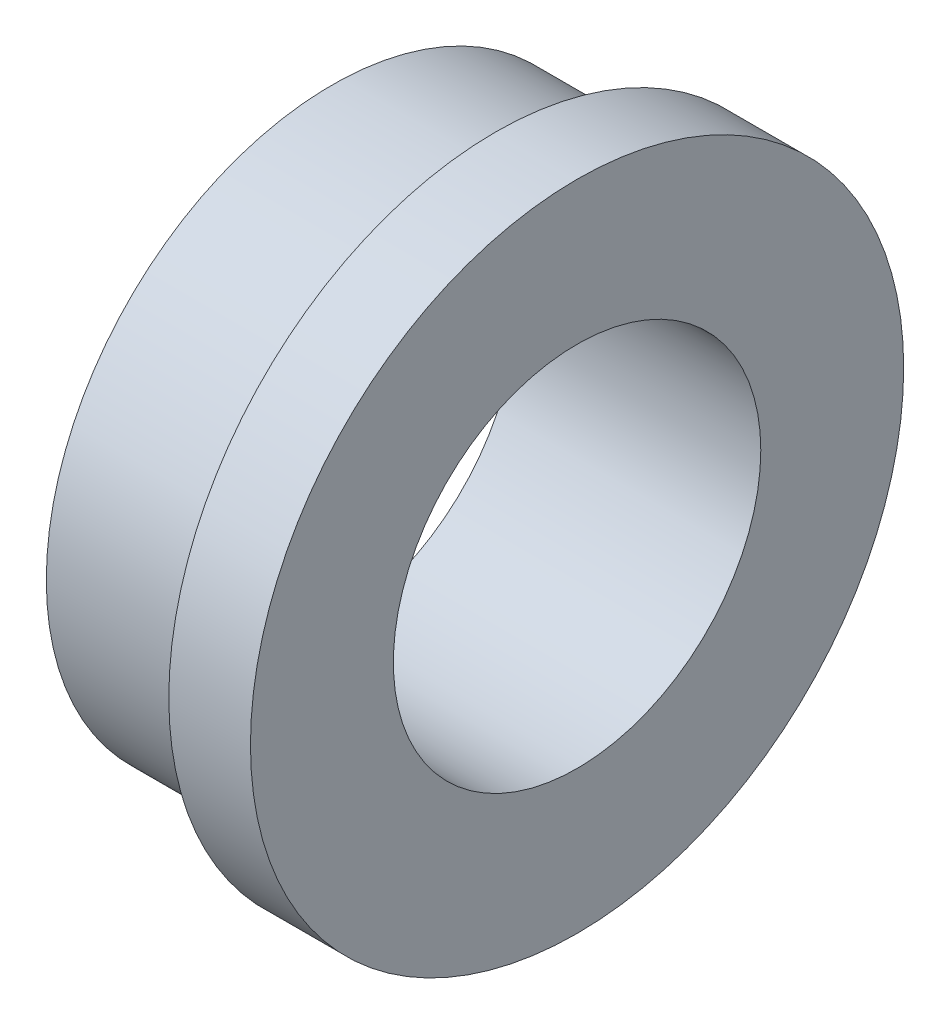
SolidWorks part; units mm, degrees
material "6061-T6 (SS)"
ref_plane "Front Plane" through (0, 0, 0) normal (0, 0, 1) x (1, 0, 0)
ref_plane "Top Plane" through (0, 0, 0) normal (0, 1, 0) x (1, 0, 0)
ref_plane "Right Plane" through (0, 0, 0) normal (1, 0, 0) x (0, 0, -1)
sketch "Sketch1" plane through (0, 0, 0) normal (0, 0, 1) x (1, 0, 0)
  line L0 (-19.05, 14.2875) -> (0, 14.2875)
  line L1 (0, 25.4) -> (-6.35, 25.4)
  line L2 (-6.35, 25.4) -> (-6.35, 22.225)
  line L3 (-6.35, 22.225) -> (-19.05, 22.225)
  line L4 (-19.05, 22.225) -> (-19.05, 14.2875)
  line L5 (0, 14.2875) -> (0, 25.4)
  line L6 (0, 0) -> (-42.9725, 0) construction
  line L7 (0, 0) -> (0, 14.2875) construction
  dimension "D1" = 6.35
  dimension "D2" = 25.4
  dimension "D3" = 19.05
  dimension "D4" = 14.2875
  dimension "D5" = 22.225
revolve "Revolve1" add sketch "Sketch1" angle 360 about L6
